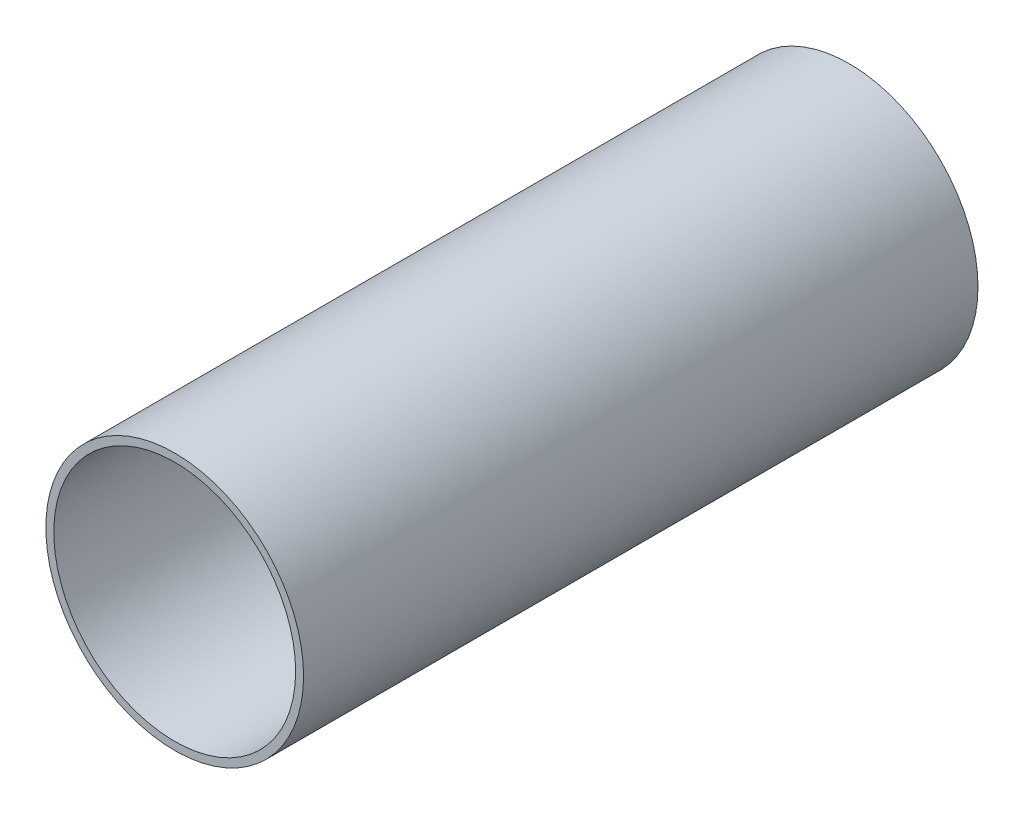
SolidWorks part; units mm, degrees
ref_plane "Front Plane" through (0, 0, 0) normal (0, 0, 1) x (1, 0, 0)
ref_plane "Top Plane" through (0, 0, 0) normal (0, 1, 0) x (1, 0, 0)
ref_plane "Right Plane" through (0, 0, 0) normal (1, 0, 0) x (0, 0, -1)
sketch "Sketch1" plane through (0, 0, 0) normal (0, 0, 1) x (1, 0, 0)
  line L0 (-360, 8688.7401) -> (-360, 1311.2599) construction
  circle A0 centre (2240, 0) radius 152.4
  dimension "D1" = 304.8
  dimension "D2" = 2600
extrude "Extrude-Thin1" add sketch "Sketch1" along normal blind 850 thin
